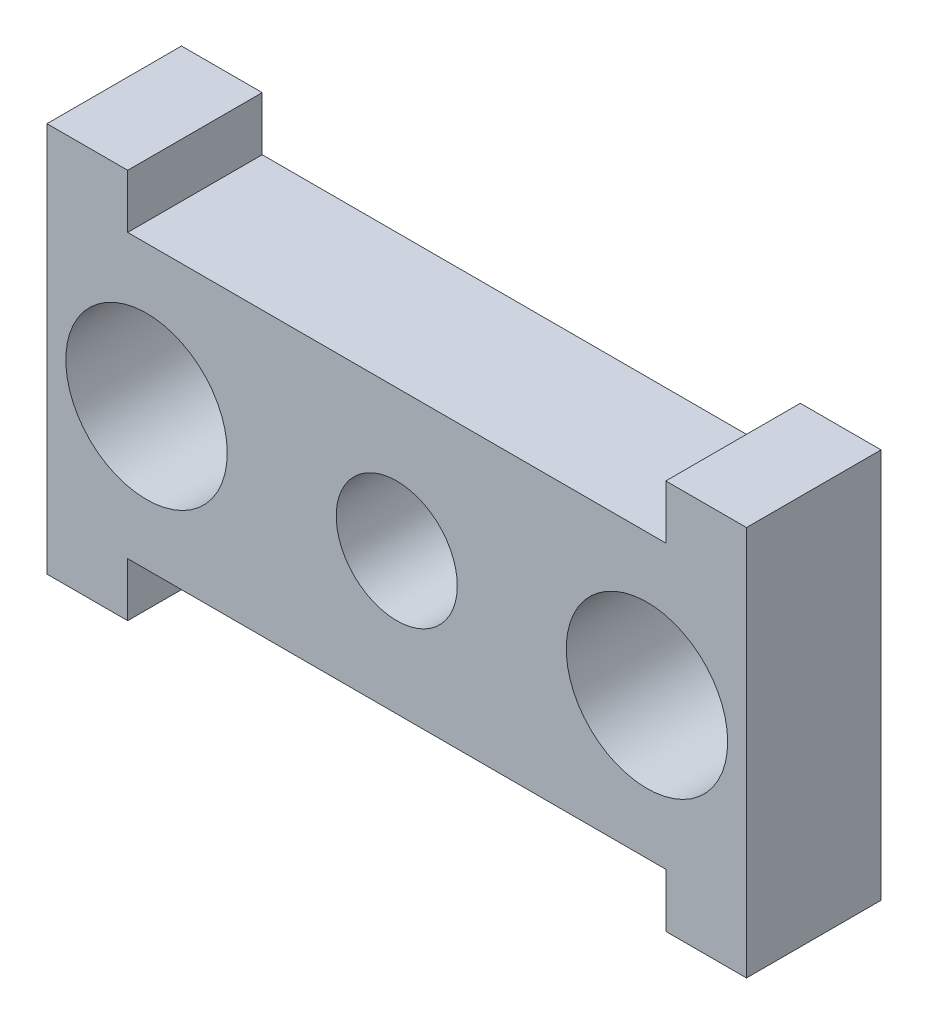
SolidWorks part; units mm, degrees
ref_plane "Front Plane" through (0, 0, 0) normal (0, 0, 1) x (1, 0, 0)
ref_plane "Top Plane" through (0, 0, 0) normal (0, 1, 0) x (1, 0, 0)
ref_plane "Right Plane" through (0, 0, 0) normal (1, 0, 0) x (0, 0, -1)
sketch "Sketch1" plane through (0, 0, 0) normal (0, 0, 1) x (1, 0, 0)
  line L0 (-13, 7.25) -> (13, -7.25) construction
  line L1 (-13, -7.25) -> (13, -7.25)
  line L2 (-13, -7.25) -> (-13, 7.25)
  line L3 (-13, 7.25) -> (13, 7.25)
  line L4 (13, -7.25) -> (13, 7.25)
  line L5 (-13, -7.25) -> (0, 0) construction
  line L6 (0, 0) -> (13, 7.25) construction
  line L7 (0, 0) -> (9.3, 0) construction
  line L8 (0, 7.25) -> (0, 0) construction
  line L9 (0, 0) -> (0, -7.25) construction
  line L10 (-10, 7.25) -> (-10, 5.25)
  line L11 (-10, 5.25) -> (10, 5.25)
  line L12 (10, 5.25) -> (10, 7.25)
  line L13 (-13, 5.25) -> (-10, 5.25) construction
  line L14 (10, 5.25) -> (13, 5.25) construction
  line L15 (10, -5.25) -> (10, -7.25)
  line L16 (-10, -7.25) -> (-10, -5.25)
  line L17 (-10, -5.25) -> (10, -5.25)
  line L18 (-10, 5.25) -> (-10, -5.25) construction
  circle A0 centre (0, 0) radius 2.25
  circle A1 centre (9.3, 0) radius 3
  circle A2 centre (-9.3, 0) radius 3
  dimension "D3" = 9.3
  dimension "D4" = 4.5
  dimension "D5" = 6
  dimension "D1" = 10.5
  dimension "D2" = 26
  dimension "D6" = 2
  dimension "D7" = 20
extrude "Boss-Extrude1" add sketch "Sketch1" along normal blind 5 contours L16 L17 L15 L1 L4 L3 L12 L11 L10 L2 A0 A1 A2
